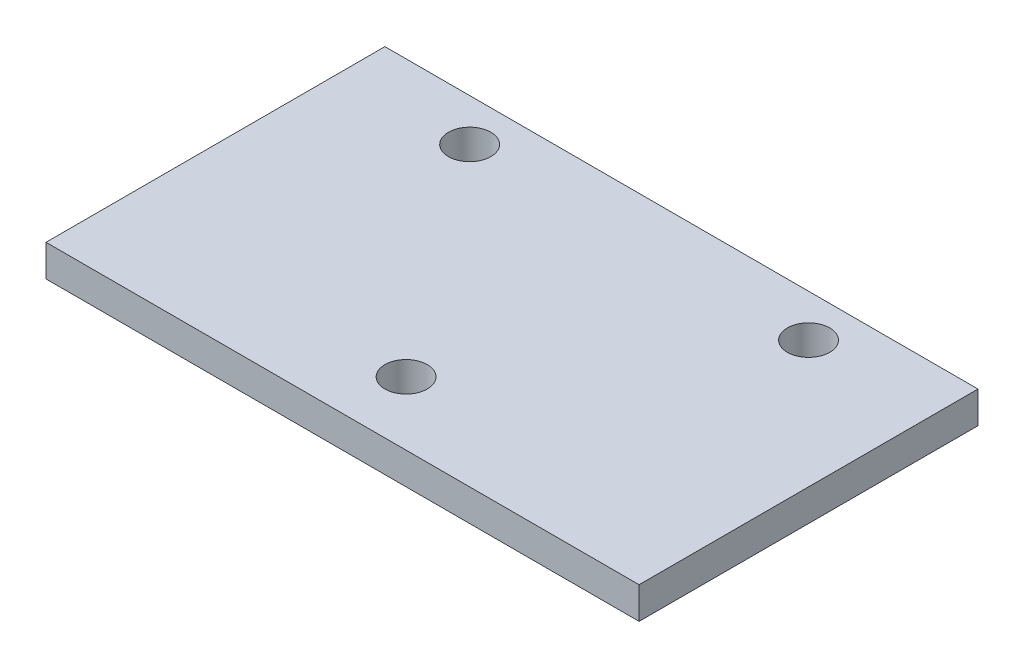
SolidWorks part; units mm, degrees
material "PW30:2:Sc:0:"
ref_plane "Front" through (0, 0, 0) normal (0, 0, 1) x (1, 0, 0)
ref_plane "Top" through (0, 0, 0) normal (0, 1, 0) x (1, 0, 0)
ref_plane "Right" through (0, 0, 0) normal (1, 0, 0) x (0, 0, -1)
sketch "Sketch1" plane through (0, 0, 0) normal (0, 1, 0) x (1, 0, 0)
  line L0 (-88.9, -50.8) -> (88.9, -50.8)
  line L1 (-88.9, -50.8) -> (-88.9, 50.8)
  line L2 (88.9, 50.8) -> (-88.9, 50.8)
  line L3 (88.9, 50.8) -> (88.9, -50.8)
  line L4 (-88.9, 50.8) -> (88.9, -50.8) construction
  dimension "D1" = 101.6
  dimension "D2" = 177.8
extrude "Plate" add sketch "Sketch1" along normal blind 9.525
sketch "Sketch2" plane through (0, 9.525, 0) normal (0, 1, 0) x (-1, 0, 0)
  line L1 (88.9, 50.8) -> (88.9, -50.8) construction
  line L2 (-88.9, -50.8) -> (88.9, -50.8) construction
  line L4 (0, -50.8) -> (0, 78.8221) construction
  circle A0 centre (50.8, -38.1) radius 6.35
  circle A1 centre (-50.8, -38.1) radius 6.35
  circle A2 centre (0, 31.75) radius 6.35
  dimension "D2" = 12.7
  dimension "D3" = 38.1
  dimension "D1" = 12.7
  dimension "D4" = 69.85
extrude "Holes" cut sketch "Sketch2" against normal through all
